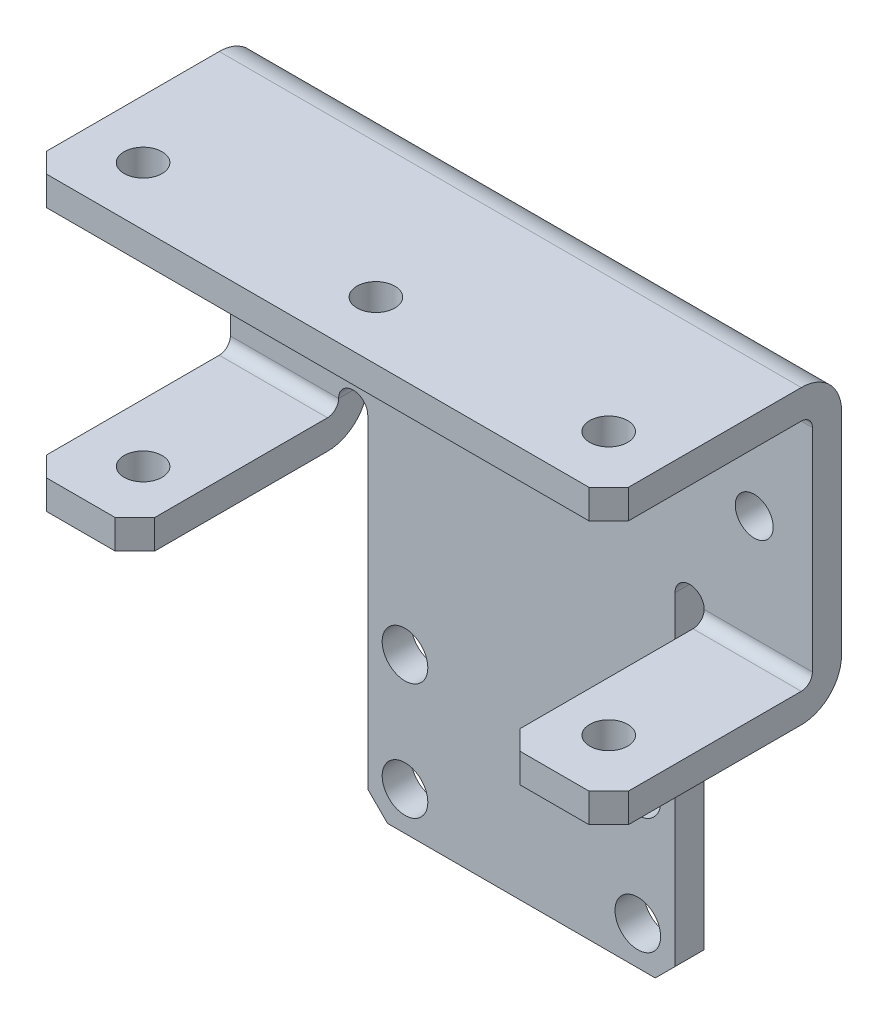
SolidWorks part; units mm, degrees
ref_plane "Front Plane" through (0, 0, 0) normal (0, 0, 1) x (1, 0, 0)
ref_plane "Top Plane" through (0, 0, 0) normal (0, 1, 0) x (1, 0, 0)
ref_plane "Right Plane" through (0, 0, 0) normal (1, 0, 0) x (0, 0, -1)
ref_plane "Plane1" through (0, 0, 0) normal (0, 0, -1) x (-1, 0, 0)
sketch "Sketch1" plane through (0, 0, 0) normal (0, 0, -1) x (-1, 0, 0)
  line L0 (-16.764, -49.0347) -> (16.764, -49.0347)
  line L1 (16.764, -49.0347) -> (16.764, -11.5443)
  line L2 (19.939, -11.5443) -> (19.939, -15.9385)
  line L3 (19.939, -15.9385) -> (31.75, -15.9385)
  line L4 (31.75, -15.9385) -> (31.75, 15.9385)
  line L5 (31.75, 15.9385) -> (-31.75, 15.9385)
  line L6 (-31.75, 15.9385) -> (-31.75, -15.9385)
  line L7 (-31.75, -15.9385) -> (-19.939, -15.9385)
  line L8 (-19.939, -15.9385) -> (-19.939, -11.5443)
  line L9 (-16.764, -11.5443) -> (-16.764, -49.0347)
  arc A0 (16.764, -11.5443) -> (19.939, -11.5443) centre (18.3515, -11.5443) cw
  arc A1 (-19.939, -11.5443) -> (-16.764, -11.5443) centre (-18.3515, -11.5443) cw
extrude "Boss-Extrude1" add sketch "Sketch1" against normal blind 3.175
sketch "Sketch2" plane through (0, 0, 3.175) normal (0, 0, 1) x (1, 0, 0)
  line L0 (31.75, 12.7635) -> (-31.75, 12.7635)
  line L1 (-31.75, 12.7635) -> (-31.75, 15.9385)
  line L2 (-31.75, 15.9385) -> (31.75, 15.9385)
  line L3 (31.75, 15.9385) -> (31.75, 12.7635)
extrude "Boss-Extrude2" add sketch "Sketch2" along normal blind 22.225
sketch "Sketch3" plane through (0, 0, 3.175) normal (0, 0, 1) x (1, 0, 0)
  line L0 (19.939, -12.7635) -> (31.75, -12.7635)
  line L1 (31.75, -12.7635) -> (31.75, -15.9385)
  line L2 (31.75, -15.9385) -> (19.939, -15.9385)
  line L3 (19.939, -15.9385) -> (19.939, -12.7635)
extrude "Boss-Extrude3" add sketch "Sketch3" along normal blind 22.225
sketch "Sketch4" plane through (0, 0, 3.175) normal (0, 0, 1) x (1, 0, 0)
  line L0 (-19.939, -15.9385) -> (-31.75, -15.9385)
  line L1 (-31.75, -15.9385) -> (-31.75, -12.7635)
  line L2 (-31.75, -12.7635) -> (-19.939, -12.7635)
  line L3 (-19.939, -12.7635) -> (-19.939, -15.9385)
extrude "Boss-Extrude4" add sketch "Sketch4" along normal blind 22.225
hole_wizard "Hole1" positions "Sketch6" profile "Sketch5" legacy
sketch "Sketch6" plane through (0, 0, 3.175) normal (0, 0, 1) x (1, 0, 0)
  point P0 (12.7, -44.831)
  point P1 (-12.7, -44.831)
  point P2 (-12.7, -32.131)
  point P3 (12.7, -32.131)
  point P4 (-12.7, 0)
  point P5 (12.7, 0)
sketch "Sketch5" plane through (12.7, -44.831, 3.175) normal (1, 0, 0) x (0, -1, 0)
  line L0 (0, 0) -> (0, 3.175)
  line L1 (0, 3.175) -> (2.4892, 3.175)
  line L2 (2.4892, 3.175) -> (2.4892, 0)
  line L3 (2.4892, 0) -> (0, 0)
  line L4 (0, 110) -> (0, -10) construction
  dimension "Diameter" = 4.9784
  dimension "Depth" = 3.175
hole_wizard "M3.5 Clearance Hole1" positions "Sketch8" profile "Sketch7" hole size "M3.5" standard "ANSI Metric"
sketch "Sketch8" plane through (0, 0, 3.175) normal (0, 0, 1) x (1, 0, 0)
  point P0 (-25.4, 0)
  point P1 (25.4, 0)
sketch "Sketch7" plane through (-25.4, 0, 3.175) normal (1, 0, 0) x (0, -1, 0)
  line L0 (0, 0) -> (0, 3.175)
  line L1 (0, 3.175) -> (2.0701, 3.175)
  line L2 (2.0701, 3.175) -> (2.0701, 0)
  line L5 (2.0701, 0) -> (0, 0)
  line L11 (0, -6.35) -> (0, 107.95) construction
  dimension "Thru Hole Dia." = 4.1402
  dimension "Thru Hole Depth" = 3.175
hole_wizard "M3.5 Clearance Hole2" positions "Sketch10" profile "Sketch9" hole size "M3.5" standard "ANSI Metric"
sketch "Sketch10" plane through (0, 15.9385, 0) normal (0, 1, 0) x (1, 0, 0)
  point P0 (25.4, -19.05)
  point P1 (0, -19.05)
  point P2 (-25.4, -19.05)
sketch "Sketch9" plane through (25.4, 15.9385, 19.05) normal (1, 0, 0) x (0, 0, 1)
  line L0 (0, 0) -> (0, 3.175)
  line L1 (0, 3.175) -> (2.0701, 3.175)
  line L2 (2.0701, 3.175) -> (2.0701, 0)
  line L5 (2.0701, 0) -> (0, 0)
  line L11 (0, -6.35) -> (0, 107.95) construction
  dimension "Thru Hole Dia." = 4.1402
  dimension "Thru Hole Depth" = 3.175
hole_wizard "M3.5 Clearance Hole3" positions "Sketch12" profile "Sketch11" hole size "M3.5" standard "ANSI Metric"
sketch "Sketch12" plane through (0, -15.9385, 0) normal (0, -1, 0) x (-1, 0, 0)
  point P0 (-25.4, -19.05)
  point P1 (25.4, -19.05)
sketch "Sketch11" plane through (25.4, -15.9385, 19.05) normal (1, 0, 0) x (0, 0, -1)
  line L0 (0, 0) -> (0, 31.877)
  line L1 (0, 31.877) -> (2.0701, 31.877)
  line L2 (2.0701, 31.877) -> (2.0701, 0)
  line L5 (2.0701, 0) -> (0, 0)
  line L11 (0, -6.35) -> (0, 107.95) construction
  dimension "Thru Hole Dia." = 4.1402
  dimension "Thru Hole Depth" = 31.877
chamfer "Chamfer1" distance 2.159 angle 45 8 edges at (-19.939, -14.351, 25.4) (31.75, 14.351, 25.4) (31.75, -14.351, 25.4) (16.764, -49.0347, 1.5875) (-31.75, 14.351, 25.4) (-31.75, -14.351, 25.4) (19.939, -14.351, 25.4) (-16.764, -49.0347, 1.5875)
fillet "Fillet1" radius 1.2192 3 edges at (25.8445, -12.7635, 3.175) (-25.8445, -12.7635, 3.175)
fillet "Fillet2" radius 4.3942 3 edges at (25.8445, -15.9385, 0) (-25.8445, -15.9385, 0) (0, 15.9385, 0)
